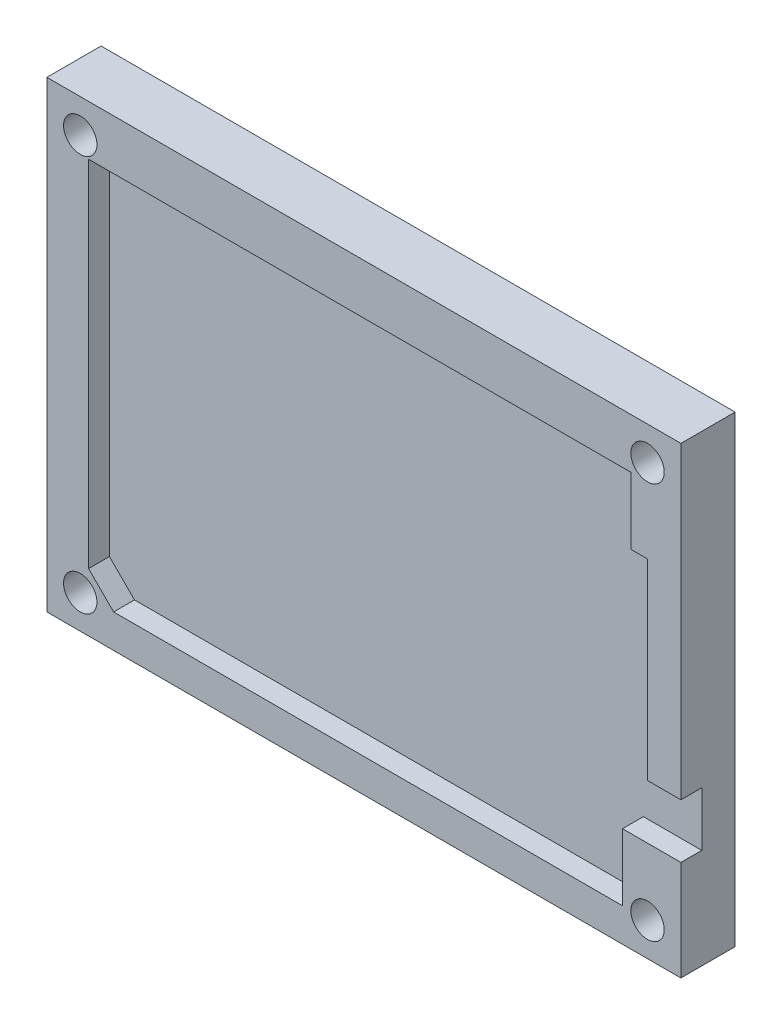
SolidWorks part; units mm, degrees
ref_plane "Front Plane" through (0, 0, 0) normal (0, 0, 1) x (1, 0, 0)
ref_plane "Top Plane" through (0, 0, 0) normal (0, 1, 0) x (1, 0, 0)
ref_plane "Right Plane" through (0, 0, 0) normal (1, 0, 0) x (0, 0, -1)
sketch "Sketch1" plane through (0, 0, 0) normal (0, 0, 1) x (1, 0, 0)
  line L1 (-38.361, 22.1591) -> (37.639, 22.1591)
  line L2 (-38.361, 22.1591) -> (-38.361, -33.3409)
  line L3 (-38.361, -33.3409) -> (37.639, -33.3409)
  line L4 (37.639, 22.1591) -> (37.639, -33.3409)
  dimension "D1" = 76
  dimension "D2" = 55.5
extrude "Boss-Extrude1" add sketch "Sketch1" along normal blind 4
sketch "Sketch2" plane through (0, 0, 4) normal (0, 0, 1) x (1, 0, 0)
  line L0 (37.639, -33.3409) -> (37.639, 22.1591) construction
  line L1 (-38.361, 22.1591) -> (37.639, 22.1591)
  line L2 (-38.361, 22.1591) -> (-38.361, 16.1591)
  line L3 (-33.361, 16.1591) -> (31.639, 16.1591)
  line L4 (37.639, 22.1591) -> (37.639, 16.1591)
  line L5 (-38.361, -33.3409) -> (37.639, -33.3409) construction
  line L7 (-38.361, 16.1591) -> (-38.361, -33.3409)
  line L8 (-38.361, -33.3409) -> (-33.361, -33.3409)
  line L9 (-33.361, 16.1591) -> (-33.361, -26.3409)
  line L10 (-33.361, -26.3409) -> (-30.361, -29.3409)
  line L11 (-33.361, -33.3409) -> (37.639, -33.3409)
  line L13 (-30.361, -29.3409) -> (30.639, -29.3409)
  line L14 (37.639, -33.3409) -> (37.639, -29.3409)
  line L16 (37.639, -29.3409) -> (37.639, -21.3409)
  line L17 (37.639, -21.3409) -> (30.639, -21.3409)
  line L18 (30.639, -29.3409) -> (30.639, -21.3409)
  line L20 (37.639, 16.1591) -> (37.639, 8.1591)
  line L21 (33.639, 8.1591) -> (31.639, 8.1591)
  line L22 (31.639, 16.1591) -> (31.639, 8.1591)
  line L24 (37.639, 8.1591) -> (37.639, -14.8409)
  line L25 (37.639, -14.8409) -> (33.639, -14.8409)
  line L26 (33.639, 8.1591) -> (33.639, -14.8409)
  dimension "D1" = 6
  dimension "D2" = 5
  dimension "D3" = 4
  dimension "D4" = 7
  dimension "D5" = 8
  dimension "D6" = 6
  dimension "D7" = 8
  dimension "D8" = 23
  dimension "D9" = 4
extrude "Boss-Extrude2" add sketch "Sketch2" along normal blind 2.5
hole_wizard "Ø4.0mm Dowel Hole1" positions "Sketch3" profile "Sketch4" hole size "Ø4.0" standard "DIN" end condition up to next
sketch "Sketch3" plane through (0, 0, 6.5) normal (0, 0, 1) x (1, 0, 0)
  line L0 (37.639, 22.1591) -> (-38.361, 22.1591) construction
  line L1 (-38.361, 22.1591) -> (-38.361, -33.3409) construction
  line L2 (37.639, -14.8409) -> (37.639, 22.1591) construction
  line L3 (-38.361, -33.3409) -> (37.639, -33.3409) construction
  line L4 (37.639, -33.3409) -> (37.639, -21.3409) construction
  point P0 (-34.361, 18.1591)
  point P2 (33.639, 18.1591)
  point P4 (33.639, -29.3409)
  point P6 (-34.361, -29.3409)
  dimension "D1" = 4
  dimension "D2" = 4
  dimension "D3" = 4
  dimension "D4" = 4
  dimension "D5" = 4
  dimension "D6" = 4
  dimension "D7" = 4
  dimension "D8" = 4
sketch "Sketch4" plane through (-34.361, 18.1591, 6.5) normal (1, 0, 0) x (0, -1, 0)
  line L0 (0, 0) -> (0, 6.5)
  line L1 (0, 6.5) -> (2, 6.5)
  line L2 (2, 6.5) -> (2, 0)
  line L5 (2, 0) -> (0, 0)
  line L11 (0, -6.35) -> (0, 107.95) construction
  dimension "Thru Hole Dia." = 4
  dimension "Thru Hole Depth" = 6.5
